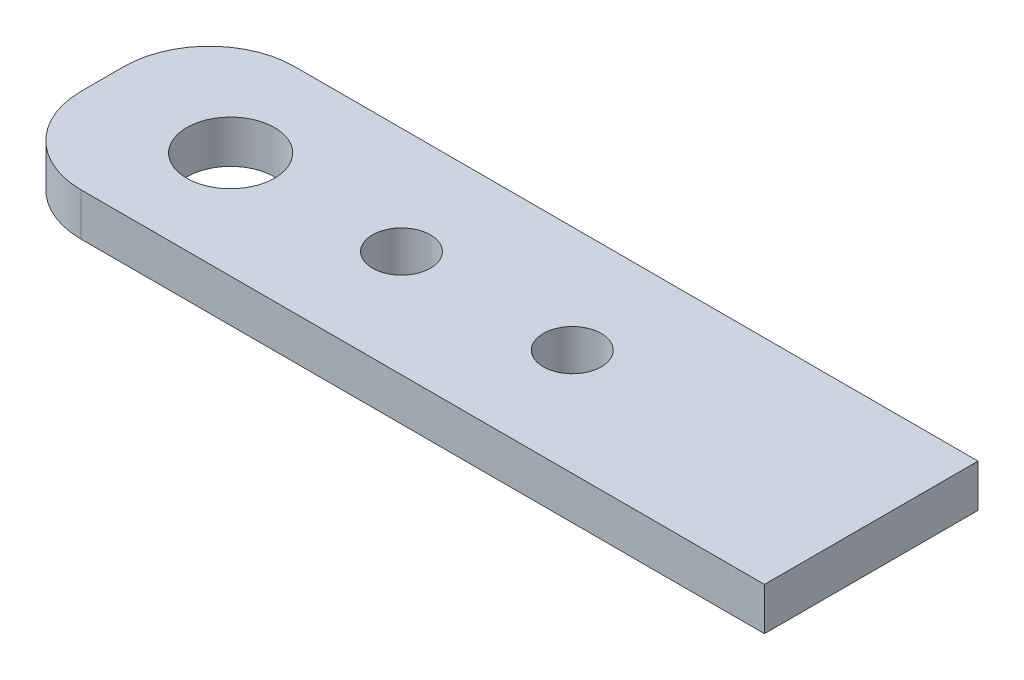
SolidWorks part; units mm, degrees
material "6061-T6 (SS)"
ref_plane "Front Plane" through (0, 0, 0) normal (0, 0, 1) x (1, 0, 0)
ref_plane "Top Plane" through (0, 0, 0) normal (0, 1, 0) x (1, 0, 0)
ref_plane "Right Plane" through (0, 0, 0) normal (1, 0, 0) x (0, 0, -1)
sketch "Sketch1" plane through (0, 0, 0) normal (0, 1, 0) x (1, 0, 0)
  line L1 (-28.575, -7.9375) -> (28.575, -7.9375)
  line L2 (-28.575, -7.9375) -> (-28.575, 7.9375)
  line L3 (-28.575, 7.9375) -> (28.575, 7.9375)
  line L4 (28.575, -7.9375) -> (28.575, 7.9375)
  line L5 (-28.575, -7.9375) -> (28.575, 7.9375) construction
  line L6 (-28.575, 7.9375) -> (28.575, -7.9375) construction
  point P0 (0, 0)
  dimension "D1" = 57.15
  dimension "D2" = 15.875
extrude "Boss-Extrude1" add sketch "Sketch1" along normal blind 3.175
hole_wizard "F (0.257) Diameter Hole1" positions "Sketch2" profile "Sketch3" hole size "F" standard "ANSI Inch" end condition through all
sketch "Sketch2" plane through (0, 3.175, 0) normal (0, 1, 0) x (1, 0, 0)
  line L1 (28.575, -7.9375) -> (28.575, 7.9375) construction
  point P0 (-19.05, 0)
  dimension "D1" = 47.625
sketch "Sketch3" plane through (-19.05, 3.175, 0) normal (1, 0, 0) x (0, 0, 1)
  line L0 (0, 0) -> (0, 3.175)
  line L1 (0, 3.175) -> (3.2639, 3.175)
  line L2 (3.2639, 3.175) -> (3.2639, 0)
  line L5 (3.2639, 0) -> (0, 0)
  line L11 (0, -6.35) -> (0, 107.95) construction
  dimension "Thru Hole Dia." = 6.5278
  dimension "Thru Hole Depth" = 3.175
fillet "Fillet1" radius 6.35 2 edges at (-28.575, 1.5875, -7.9375) (-28.575, 1.5875, 7.9375)
hole_wizard "#18 (0.1695) Diameter Hole1" positions "Sketch4" profile "Sketch5" hole size "#18" standard "ANSI Inch" end condition through all
sketch "Sketch4" plane through (0, 3.175, 0) normal (0, 1, 0) x (1, 0, 0)
  line L0 (28.575, 0) -> (-28.575, 0) construction
  line L1 (28.575, -7.9375) -> (28.575, 7.9375) construction
  line L2 (-28.575, 1.5875) -> (-28.575, -1.5875) construction
  point P0 (-6.35, 0)
  point P2 (6.35, 0)
  dimension "D1" = 34.925
  dimension "D2" = 22.225
sketch "Sketch5" plane through (-6.35, 3.175, 0) normal (1, 0, 0) x (0, 0, 1)
  line L0 (0, 0) -> (0, 3.175)
  line L1 (0, 3.175) -> (2.1526, 3.175)
  line L2 (2.1526, 3.175) -> (2.1526, 0)
  line L5 (2.1526, 0) -> (0, 0)
  line L11 (0, -6.35) -> (0, 107.95) construction
  dimension "Thru Hole Dia." = 4.3053
  dimension "Thru Hole Depth" = 3.175
